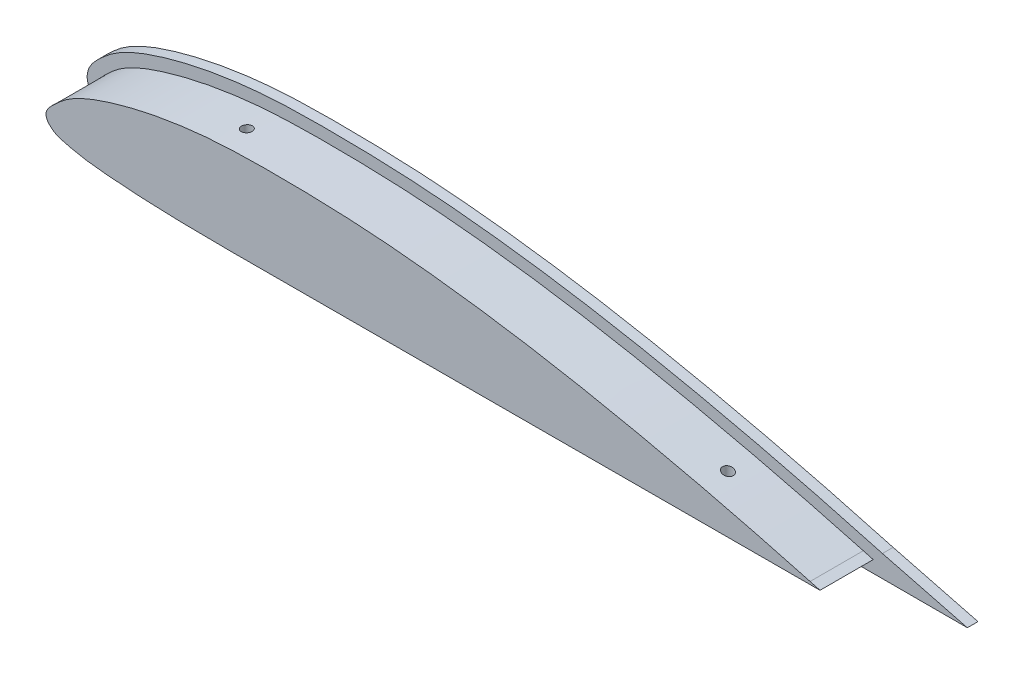
SolidWorks part; units mm, degrees
ref_plane "Front Plane" through (0, 0, 0) normal (0, 0, 1) x (1, 0, 0)
ref_plane "Top Plane" through (0, 0, 0) normal (0, 1, 0) x (1, 0, 0)
ref_plane "Right Plane" through (0, 0, 0) normal (1, 0, 0) x (0, 0, -1)
sketch "Sketch1" plane through (0, 0, 0) normal (0, 0, 1) x (1, 0, 0)
  line L4 (-17.7123, -35.5758) -> (-1.2238, -35.5758)
  line L5 (-1.2238, -35.5758) -> (-17.1809, -31.471)
  spline S2 degree 3 poles (-17.1809, -31.471) (-20.2056, -30.6413) (-26.2535, -28.9879) (-38.4291, -25.8815) (-53.7325, -22.3522) (-72.2469, -18.7478) (-87.8416, -16.5256) (-100.3857, -15.2975) (-109.8486, -14.7321) (-119.2946, -14.543) (-127.1783, -14.5697) (-133.5392, -14.9033) (-138.3167, -15.385) (-143.0523, -16.1027) (-146.9743, -16.888) (-150.0976, -17.6614) (-152.4204, -18.3224) (-154.721, -19.0554) (-157.0283, -19.9018) (-158.9383, -20.7504) (-160.4449, -21.552) (-161.5667, -22.2428) (-162.6439, -23.0198) (-163.6502, -23.8812) (-164.3836, -24.5581) (-165.0259, -25.1979) (-165.5202, -25.7567) (-166.014, -26.4401) (-166.3895, -27.1745) (-166.6066, -27.9625) (-166.6593, -28.6499) (-166.5912, -29.2918) (-166.3998, -29.9297) (-166.1734, -30.4043) (-165.8214, -30.9817) (-165.3347, -31.5618) (-164.7206, -32.1221) (-164.0346, -32.6145) (-163.2893, -33.0085) (-162.336, -33.3878) (-161.2239, -33.6821) (-160.1044, -33.9422) (-158.884, -34.2133) (-157.6571, -34.434) (-156.0223, -34.6701) (-154.0153, -34.8738) (-151.6689, -35.074) (-148.5037, -35.3123) (-144.5593, -35.5212) (-139.8292, -35.6754) (-135.1087, -35.7537) (-130.3968, -35.7823) (-125.692, -35.779) (-119.4312, -35.7563) (-111.6117, -35.7425) (-102.2196, -35.7297) (-92.8302, -35.7113) (-83.4404, -35.6942) (-70.9208, -35.671) (-55.2715, -35.6437) (-36.4921, -35.6094) (-23.9722, -35.5877) (-17.7123, -35.5758) knots 0 0 0 0 0.03125 0.0625 0.125 0.1875 0.25 0.28125 0.3125 0.34375 0.375 0.390625 0.40625 0.421875 0.4375 0.445312 0.453125 0.460938 0.46875 0.476562 0.480469 0.484375 0.488281 0.492188 0.496094 0.498047 0.5 0.501953 0.503906 0.504883 0.505859 0.506836 0.507812 0.508789 0.509766 0.511719 0.513672 0.515625 0.517578 0.519531 0.523438 0.527344 0.53125 0.535156 0.539062 0.546875 0.554688 0.5625 0.578125 0.59375 0.609375 0.625 0.640625 0.65625 0.6875 0.71875 0.75 0.78125 0.8125 0.875 0.9375 1 1 1 1
extrude "Boss-Extrude1" add sketch "Sketch1" along normal blind 2
sketch "Sketch4" plane through (0, 0, 0) normal (0, 0, -1) x (-1, 0, 0)
  line L0 (17.7099, -33.3998) -> (17.7161, -33.5758)
  spline S0 degree 3 poles (-1752.0663, 4617.1234) (-284.9942, -178.3645) (-137.8472, -74.9484) (27.42, -30.7701) (33.2455, -29.2637) (39.0817, -27.8262) (45.8902, -26.2262) (52.6942, -24.7026) (63.3939, -22.5012) (76.0469, -20.2024) (89.7256, -18.3313) (99.5157, -17.3935) (108.3249, -16.8174) (114.2044, -16.6258) (121.0664, -16.5619) (125.9741, -16.5715) (130.8853, -16.7446) (135.8084, -17.114) (139.7519, -17.6021) (144.693, -18.4439) (148.66, -19.3156) (152.605, -20.4616) (155.6094, -21.4769) (158.1057, -22.5462) (160.0998, -23.6553) (161.5146, -24.6573) (162.5844, -25.6177) (163.4024, -26.3911) (163.9246, -26.9592) (164.3139, -27.5109) (164.5291, -27.9473) (164.6657, -28.4647) (164.6332, -28.894) (164.4974, -29.2715) (164.3478, -29.5731) (164.0382, -30.0159) (163.5591, -30.4905) (162.8052, -31.0401) (161.7243, -31.5017) (160.3363, -31.8322) (158.8785, -32.1754) (157.4161, -32.4511) (155.4643, -32.7272) (153.018, -32.9537) (150.0845, -33.1959) (144.2141, -33.5688) (134.4114, -33.8206) (120.6848, -33.7522) (107.9367, -33.7395) (92.2462, -33.7104) (76.5556, -33.6814) (60.8651, -33.653) (50.0778, -33.6346) (41.2519, -33.6178) (32.426, -33.6028) (-377.6366, -32.8236) (-784.7691, -38.6184) (-1180.3743, 4682.5216) knots -1.657819 -1.657819 -1.657819 -1.657819 0.020105 0.030145 0.050191 0.08018 0.090156 0.12002 0.149793 0.199219 0.248396 0.287604 0.297393 0.336535 0.346322 0.365908 0.385531 0.395376 0.415192 0.425184 0.445412 0.455711 0.466191 0.477055 0.482787 0.488946 0.494316 0.497126 0.500187 0.502001 0.50385 0.50502 0.507318 0.507987 0.509024 0.510668 0.513358 0.515716 0.519949 0.524973 0.529954 0.534903 0.539824 0.54963 0.559425 0.569214 0.608356 0.657307 0.706263 0.735637 0.813967 0.862923 0.892297 0.92167 0.951044 0.980418 5.015871 5.015871 5.015871 5.015871 only from (17.7099, -33.3998) to (17.7161, -33.5758) construction
  spline S1 degree 3 poles (17.7099, -33.3998) (19.6519, -32.8671) (22.5636, -32.0683) (27.42, -30.7701) (33.2455, -29.2637) (39.0817, -27.8262) (45.8902, -26.2262) (52.6942, -24.7026) (63.3939, -22.5012) (76.0469, -20.2024) (89.7256, -18.3313) (99.5157, -17.3935) (108.3249, -16.8174) (114.2044, -16.6258) (121.0664, -16.5619) (125.9741, -16.5715) (130.8853, -16.7446) (135.8084, -17.114) (139.7519, -17.6021) (144.693, -18.4439) (148.66, -19.3156) (152.605, -20.4616) (155.6094, -21.4769) (158.1057, -22.5462) (160.0998, -23.6553) (161.5146, -24.6573) (162.5844, -25.6177) (163.4024, -26.3911) (163.9246, -26.9592) (164.3139, -27.5109) (164.5291, -27.9473) (164.6657, -28.4647) (164.6332, -28.894) (164.4974, -29.2715) (164.3478, -29.5731) (164.0382, -30.0159) (163.5591, -30.4905) (162.8052, -31.0401) (161.7243, -31.5017) (160.3363, -31.8322) (158.8785, -32.1754) (157.4161, -32.4511) (155.4643, -32.7272) (153.018, -32.9537) (150.0845, -33.1959) (144.2141, -33.5688) (134.4114, -33.8206) (120.6848, -33.7522) (107.9367, -33.7395) (92.2462, -33.7104) (76.5556, -33.6814) (60.8651, -33.653) (50.0778, -33.6346) (41.2519, -33.6178) (32.426, -33.6028) (24.5807, -33.5879) (19.6774, -33.5795) (17.7161, -33.5758) knots 0 0 0 0 0.020105 0.030145 0.050191 0.08018 0.090156 0.12002 0.149793 0.199219 0.248396 0.287604 0.297393 0.336535 0.346322 0.365908 0.385531 0.395376 0.415192 0.425184 0.445412 0.455711 0.466191 0.477055 0.482787 0.488946 0.494316 0.497126 0.500187 0.502001 0.50385 0.50502 0.507318 0.507987 0.509024 0.510668 0.513358 0.515716 0.519949 0.524973 0.529954 0.534903 0.539824 0.54963 0.559425 0.569214 0.608356 0.657307 0.706263 0.735637 0.813967 0.862923 0.892297 0.92167 0.951044 0.980418 1 1 1 1
extrude "Boss-Extrude2" add sketch "Sketch4" along normal blind 10
sketch "Sketch5" plane through (0, 0, 0) normal (0, 1, 0) x (1, 0, 0)
  line L0 (-17.1809, 0) -> (-166.6394, 0) construction
  circle A0 centre (-131.6394, 5) radius 1
  circle A1 centre (-41.2238, 5) radius 1
  dimension "D1" = 5
extrude "Cut-Extrude1" cut sketch "Sketch5" against normal through all
ref_plane "Plane1" through (0, 0, 12) normal (0, 0, 1) x (1, 0, 0)
sketch "Sketch6" plane through (0, 0, -10) normal (0, 0, -1) x (-1, 0, 0)
  line L2 (1.2238, -35.5758) -> (17.7123, -35.5758)
  line L3 (17.1809, -31.471) -> (1.2238, -35.5758)
  line L4 (1.2238, -35.5758) -> (17.7123, -35.5758)
  line L5 (17.1809, -31.471) -> (1.2238, -35.5758)
  line L6 (18.9126, -33.3281) -> (20.7104, -33.3312)
  line L7 (20.7758, -32.8192) -> (18.9126, -33.3281)
  line L8 (18.9126, -33.3281) -> (20.7104, -33.3312)
  line L9 (20.7758, -32.8192) -> (18.9126, -33.3281)
  spline S1 degree 3 poles (-2153.0812, 2876.623) (-1572.464, -37.7215) (-761.1411, -34.1514) (55.2715, -35.6437) (70.9208, -35.671) (83.4404, -35.6942) (92.8302, -35.7113) (102.2196, -35.7297) (111.6117, -35.7425) (119.4312, -35.7563) (125.692, -35.779) (130.3968, -35.7823) (135.1087, -35.7537) (139.8292, -35.6754) (144.5593, -35.5212) (148.5037, -35.3123) (151.6689, -35.074) (154.0153, -34.8738) (156.0223, -34.6701) (157.6571, -34.434) (158.884, -34.2133) (160.1044, -33.9422) (161.2239, -33.6821) (162.336, -33.3878) (163.2893, -33.0085) (164.0346, -32.6145) (164.7206, -32.1221) (165.3347, -31.5618) (165.8214, -30.9817) (166.1734, -30.4043) (166.3998, -29.9297) (166.5912, -29.2918) (166.6593, -28.6499) (166.6066, -27.9625) (166.3895, -27.1745) (166.014, -26.4401) (165.5202, -25.7567) (165.0259, -25.1979) (164.3836, -24.5581) (163.6502, -23.8812) (162.6439, -23.0198) (161.5667, -22.2428) (160.4449, -21.552) (158.9383, -20.7504) (157.0283, -19.9018) (154.721, -19.0554) (152.4204, -18.3224) (150.0976, -17.6614) (146.9743, -16.888) (143.0523, -16.1027) (138.3167, -15.385) (133.5392, -14.9033) (127.1783, -14.5697) (119.2946, -14.543) (109.8486, -14.7321) (100.3857, -15.2975) (87.8416, -16.5256) (72.2469, -18.7478) (53.7325, -22.3522) (38.4291, -25.8815) (-138.2007, -70.9462) (-277.4971, -193.116) (-2167.8347, 3289.5843) knots -7.963834 -7.963834 -7.963834 -7.963834 0.0625 0.125 0.1875 0.21875 0.25 0.28125 0.3125 0.34375 0.359375 0.375 0.390625 0.40625 0.421875 0.4375 0.445312 0.453125 0.460938 0.464844 0.46875 0.472656 0.476562 0.480469 0.482422 0.484375 0.486328 0.488281 0.490234 0.491211 0.492188 0.493164 0.494141 0.495117 0.496094 0.498047 0.5 0.501953 0.503906 0.507812 0.511719 0.515625 0.519531 0.523438 0.53125 0.539062 0.546875 0.554688 0.5625 0.578125 0.59375 0.609375 0.625 0.65625 0.6875 0.71875 0.75 0.8125 0.875 0.9375 0.96875 2.688371 2.688371 2.688371 2.688371 only from (17.7123, -35.5758) to (17.1809, -31.471)
  spline S2 degree 3 poles (17.7123, -35.5758) (23.9722, -35.5877) (36.4921, -35.6094) (55.2715, -35.6437) (70.9208, -35.671) (83.4404, -35.6942) (92.8302, -35.7113) (102.2196, -35.7297) (111.6117, -35.7425) (119.4312, -35.7563) (125.692, -35.779) (130.3968, -35.7823) (135.1087, -35.7537) (139.8292, -35.6754) (144.5593, -35.5212) (148.5037, -35.3123) (151.6689, -35.074) (154.0153, -34.8738) (156.0223, -34.6701) (157.6571, -34.434) (158.884, -34.2133) (160.1044, -33.9422) (161.2239, -33.6821) (162.336, -33.3878) (163.2893, -33.0085) (164.0346, -32.6145) (164.7206, -32.1221) (165.3347, -31.5618) (165.8214, -30.9817) (166.1734, -30.4043) (166.3998, -29.9297) (166.5912, -29.2918) (166.6593, -28.6499) (166.6066, -27.9625) (166.3895, -27.1745) (166.014, -26.4401) (165.5202, -25.7567) (165.0259, -25.1979) (164.3836, -24.5581) (163.6502, -23.8812) (162.6439, -23.0198) (161.5667, -22.2428) (160.4449, -21.552) (158.9383, -20.7504) (157.0283, -19.9018) (154.721, -19.0554) (152.4204, -18.3224) (150.0976, -17.6614) (146.9743, -16.888) (143.0523, -16.1027) (138.3167, -15.385) (133.5392, -14.9033) (127.1783, -14.5697) (119.2946, -14.543) (109.8486, -14.7321) (100.3857, -15.2975) (87.8416, -16.5256) (72.2469, -18.7478) (53.7325, -22.3522) (38.4291, -25.8815) (26.2535, -28.9879) (20.2056, -30.6413) (17.1809, -31.471) knots 0 0 0 0 0.0625 0.125 0.1875 0.21875 0.25 0.28125 0.3125 0.34375 0.359375 0.375 0.390625 0.40625 0.421875 0.4375 0.445312 0.453125 0.460938 0.464844 0.46875 0.472656 0.476562 0.480469 0.482422 0.484375 0.486328 0.488281 0.490234 0.491211 0.492188 0.493164 0.494141 0.495117 0.496094 0.498047 0.5 0.501953 0.503906 0.507812 0.511719 0.515625 0.519531 0.523438 0.53125 0.539062 0.546875 0.554688 0.5625 0.578125 0.59375 0.609375 0.625 0.65625 0.6875 0.71875 0.75 0.8125 0.875 0.9375 0.96875 1 1 1 1
  spline S3 degree 3 poles (-3436.2373, -1627.6892) (-2305.1312, -28.116) (-1126.802, -31.2687) (57.5062, -33.3974) (75.9041, -33.4302) (91.2357, -33.4581) (103.501, -33.4821) (112.6996, -33.4933) (121.8997, -33.5135) (129.5643, -33.5416) (135.6938, -33.4965) (140.2896, -33.4129) (144.8816, -33.2544) (148.7043, -33.0445) (151.7562, -32.8086) (154.0468, -32.612) (156.3244, -32.3721) (158.2017, -32.0635) (159.6865, -31.7286) (160.8085, -31.4684) (161.8941, -31.1685) (162.8943, -30.7063) (163.7412, -30.0102) (164.3939, -29.124) (164.4205, -28.1315) (163.8227, -27.2022) (163.0533, -26.3936) (162.2102, -25.6147) (161.354, -24.8725) (160.1381, -23.9771) (158.4982, -23.0289) (156.4202, -22.0862) (154.2786, -21.2835) (151.3713, -20.341) (147.6845, -19.3393) (143.1896, -18.415) (138.656, -17.7009) (134.0946, -17.2061) (127.9852, -16.8421) (120.3257, -16.7864) (111.1333, -16.9422) (101.9566, -17.4342) (92.804, -18.2836) (83.678, -19.3955) (71.5573, -21.2159) (56.4987, -24.0757) (-302.6464, -105.0181) (-575.0639, -524.144) (-1267.5985, 3633.4875) knots -11.630495 -11.630495 -11.630495 -11.630495 0.071582 0.132813 0.194043 0.255273 0.285888 0.316503 0.347118 0.377734 0.393041 0.408349 0.423656 0.438964 0.446618 0.454271 0.461925 0.469579 0.473406 0.477233 0.48106 0.484887 0.488713 0.49254 0.496367 0.500194 0.504021 0.507848 0.511675 0.515502 0.523155 0.530809 0.538463 0.546117 0.561424 0.576732 0.592039 0.607347 0.622655 0.65327 0.683885 0.7145 0.745115 0.77573 0.806345 0.867576 0.928806 4.483446 4.483446 4.483446 4.483446 only from (20.7104, -33.3312) to (20.7758, -32.8192)
  spline S4 degree 3 poles (20.7104, -33.3312) (26.843, -33.3421) (39.1083, -33.3643) (57.5062, -33.3974) (75.9041, -33.4302) (91.2357, -33.4581) (103.501, -33.4821) (112.6996, -33.4933) (121.8997, -33.5135) (129.5643, -33.5416) (135.6938, -33.4965) (140.2896, -33.4129) (144.8816, -33.2544) (148.7043, -33.0445) (151.7562, -32.8086) (154.0468, -32.612) (156.3244, -32.3721) (158.2017, -32.0635) (159.6865, -31.7286) (160.8085, -31.4684) (161.8941, -31.1685) (162.8943, -30.7063) (163.7412, -30.0102) (164.3939, -29.124) (164.4205, -28.1315) (163.8227, -27.2022) (163.0533, -26.3936) (162.2102, -25.6147) (161.354, -24.8725) (160.1381, -23.9771) (158.4982, -23.0289) (156.4202, -22.0862) (154.2786, -21.2835) (151.3713, -20.341) (147.6845, -19.3393) (143.1896, -18.415) (138.656, -17.7009) (134.0946, -17.2061) (127.9852, -16.8421) (120.3257, -16.7864) (111.1333, -16.9422) (101.9566, -17.4342) (92.804, -18.2836) (83.678, -19.3955) (71.5573, -21.2159) (56.4987, -24.0757) (38.5575, -28.1192) (26.6893, -31.2044) (20.7758, -32.8192) knots 0.010352 0.010352 0.010352 0.010352 0.071582 0.132813 0.194043 0.255273 0.285888 0.316503 0.347118 0.377734 0.393041 0.408349 0.423656 0.438964 0.446618 0.454271 0.461925 0.469579 0.473406 0.477233 0.48106 0.484887 0.488713 0.49254 0.496367 0.500194 0.504021 0.507848 0.511675 0.515502 0.523155 0.530809 0.538463 0.546117 0.561424 0.576732 0.592039 0.607347 0.622655 0.65327 0.683885 0.7145 0.745115 0.77573 0.806345 0.867576 0.928806 0.990036 0.990036 0.990036 0.990036
  dimension "D1" = 0
  dimension "D2" = 0
extrude "Cut-Extrude2" cut sketch "Sketch6" against normal up to surface (10 mm away) up to face at (-11.9504, -33.5234, 0)
mirror "Mirror1" about plane through (-163.9552, -27.0228, -10) normal (0, 0, 1)
delete or keep bodies "Body-Delete/Keep 1" type delete bodies bodies 105
